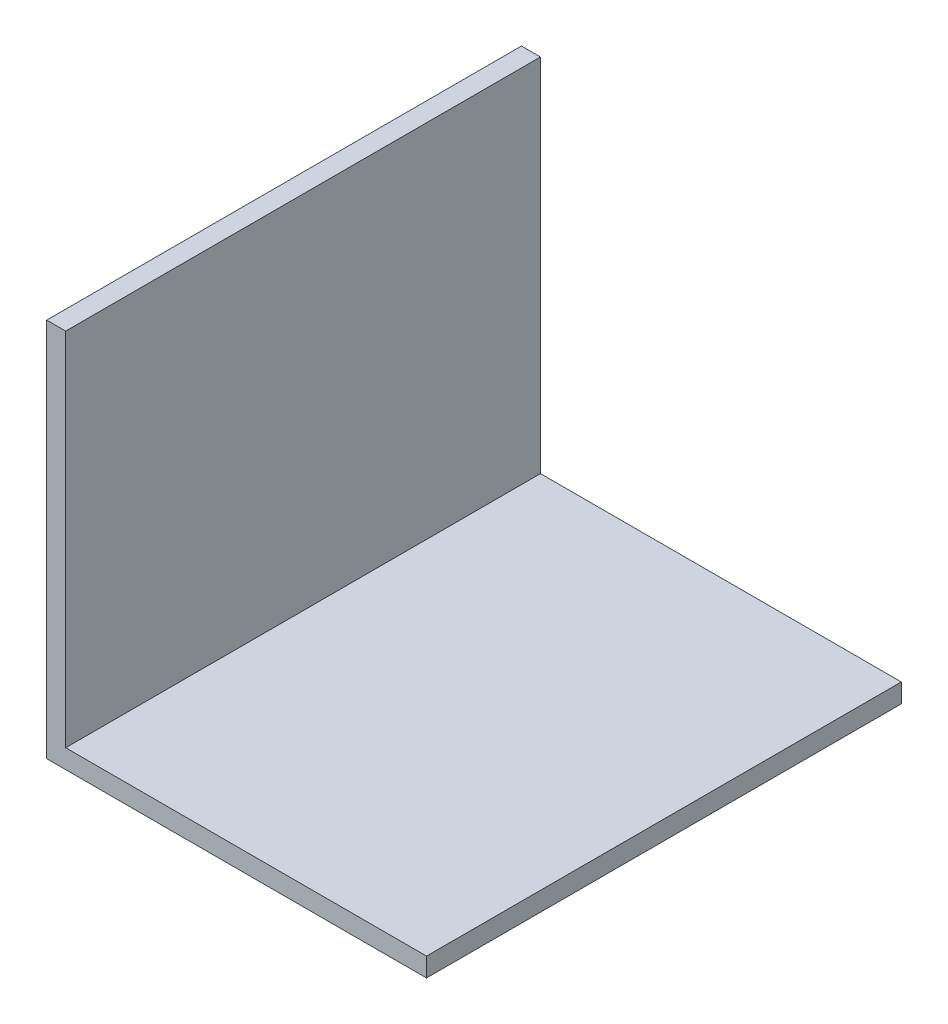
SolidWorks part; units mm, degrees
ref_plane "Plan de face" through (0, 0, 0) normal (0, 0, 1) x (1, 0, 0)
ref_plane "Plan de dessus" through (0, 0, 0) normal (0, 1, 0) x (1, 0, 0)
ref_plane "Plan de droite" through (0, 0, 0) normal (1, 0, 0) x (0, 0, -1)
sketch "Esquisse1" plane through (0, 0, 0) normal (0, 0, 1) x (1, 0, 0)
  line L0 (0, 0) -> (40, 0)
  line L1 (40, 0) -> (40, 2)
  line L2 (40, 2) -> (2, 2)
  line L3 (2, 2) -> (2, 40)
  line L4 (2, 40) -> (0, 40)
  line L5 (0, 40) -> (0, 0)
  dimension "D1" = 40
  dimension "D2" = 40
  dimension "D3" = 2
  dimension "D4" = 2
extrude "Boss.-Extru.1" add sketch "Esquisse1" along normal blind 50 contours L0 L1 L2 L3 L4 L5
